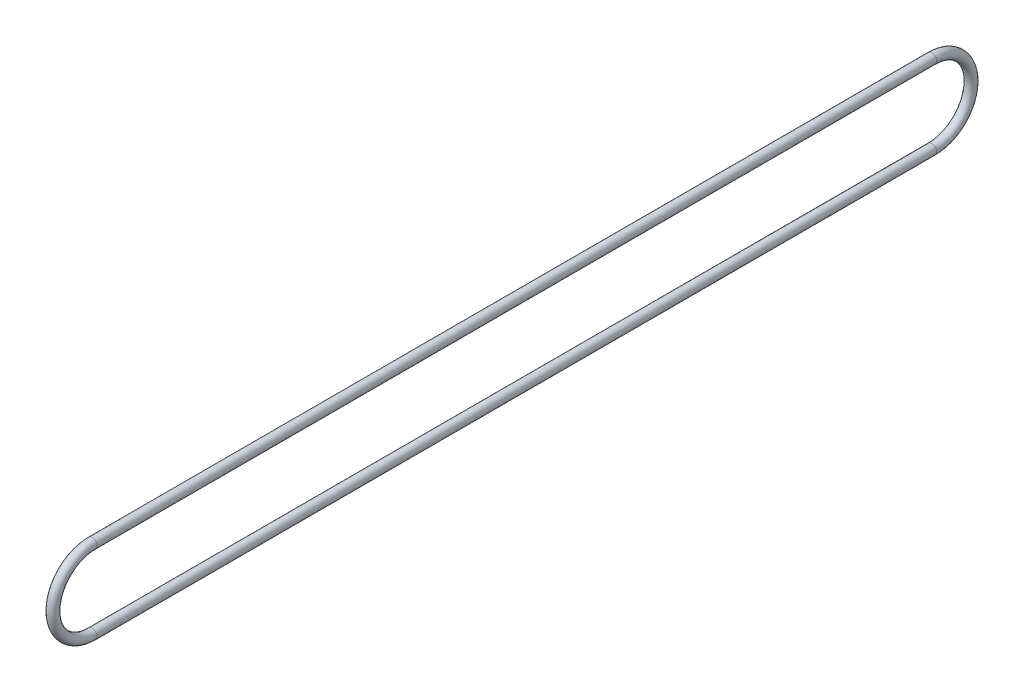
SolidWorks part; units mm, degrees
ref_plane "Front Plane" through (0, 0, 0) normal (0, 0, 1) x (1, 0, 0)
ref_plane "Top Plane" through (0, 0, 0) normal (0, 1, 0) x (1, 0, 0)
ref_plane "Right Plane" through (0, 0, 0) normal (1, 0, 0) x (0, 0, -1)
sketch "Sketch1" plane through (0, 0, 0) normal (1, 0, 0) x (0, 0, -1)
  line L0 (0, 0) -> (271.4625, 0) construction
  line L1 (0, 12.7) -> (271.4625, 12.7)
  line L2 (0, -12.7) -> (271.4625, -12.7)
  arc A0 (0, 12.7) -> (0, -12.7) centre (0, 0) ccw
  arc A1 (271.4625, -12.7) -> (271.4625, 12.7) centre (271.4625, 0) ccw
  point P3 (135.7312, 0)
  dimension "D2" = 12.7
  dimension "D1" = 271.4625
sketch "Sketch2" plane through (0, 0, 0) normal (0, 0, 1) x (1, 0, 0)
  line L0 (0, -12.7) -> (0, 12.7) construction
  circle A0 centre (0, 12.7) radius 1.5875
  dimension "D1" = 3.175
sweep "Sweep1" add profiles "Sketch2" path "Sketch1"
